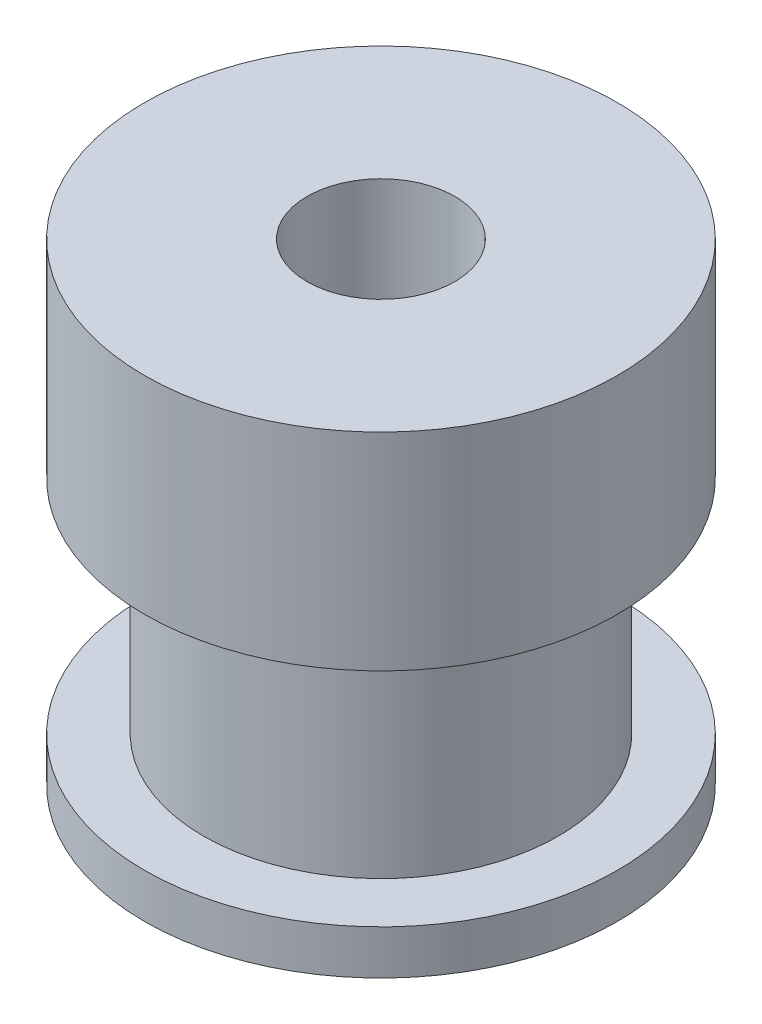
SolidWorks part; units mm, degrees
ref_plane "Front Plane" through (0, 0, 0) normal (0, 0, 1) x (1, 0, 0)
ref_plane "Top Plane" through (0, 0, 0) normal (0, 1, 0) x (1, 0, 0)
ref_plane "Right Plane" through (0, 0, 0) normal (1, 0, 0) x (0, 0, -1)
sketch "Sketch1" plane through (0, 0, 0) normal (0, 1, 0) x (1, 0, 0)
  circle A0 centre (0, 0) radius 8
  circle A1 centre (0, 0) radius 2.5
  dimension "D1" = 16
  dimension "D2" = 5
extrude "Boss-Extrude1" add sketch "Sketch1" along normal blind 16
sketch "Sketch2" plane through (0, 16, 0) normal (0, 1, 0) x (1, 0, 0)
  circle A0 centre (0, 0) radius 6
  circle A1 centre (0, 0) radius 8
  circle A2 centre (0, 0) radius 8 construction
  dimension "D1" = 12
extrude "Cut-Extrude1" cut sketch "Sketch2" against normal blind 7.5 from offset 7
